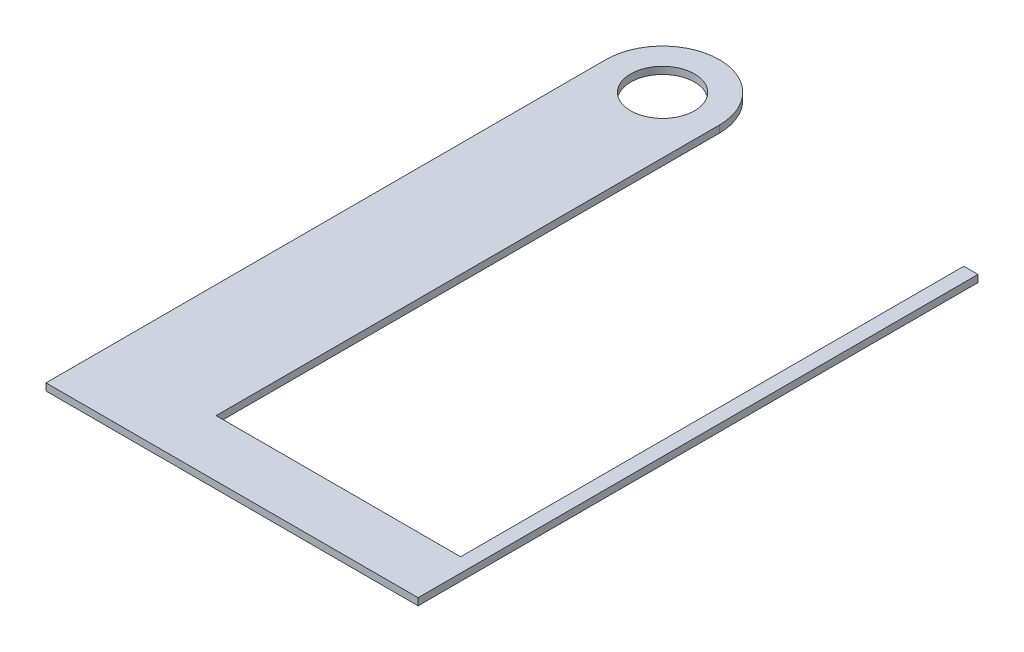
SolidWorks part; units mm, degrees
ref_plane "Front" through (0, 0, 0) normal (0, 0, 1) x (1, 0, 0)
ref_plane "Top" through (0, 0, 0) normal (0, 1, 0) x (1, 0, 0)
ref_plane "Right" through (0, 0, 0) normal (1, 0, 0) x (0, 0, -1)
sketch "Sketch1" plane through (0, 0, 0) normal (0, 1, 0) x (1, 0, 0)
  line L0 (-25.4, 0) -> (-25.4, -250.825)
  line L1 (-25.4, -250.825) -> (141.2875, -250.825)
  line L2 (141.2875, -250.825) -> (141.2875, 0)
  line L3 (141.2875, 0) -> (134.9375, 0)
  line L4 (134.9375, 0) -> (134.9375, -225.425)
  line L5 (134.9375, -225.425) -> (25.4, -225.425)
  line L6 (25.4, -225.425) -> (25.4, 0)
  line L8 (33.3375, -225.425) -> (134.9375, -225.425) construction
  line L9 (33.3375, -225.425) -> (33.3375, 76.2) construction
  line L10 (33.3375, 76.2) -> (134.9375, 76.2) construction
  line L11 (134.9375, -225.425) -> (134.9375, 76.2) construction
  line L12 (33.3375, -225.425) -> (134.9375, 76.2) construction
  line L13 (33.3375, 76.2) -> (134.9375, -225.425) construction
  circle A0 centre (0, 0) radius 14.3129
  arc A1 (25.4, 0) -> (-25.4, 0) centre (0, 0) ccw
  circle A2 centre (0, 0) radius 38.1 construction
  point P5 (84.1375, -74.6125)
  point P17 (134.9375, -250.825)
  dimension "D1" = 25.4
  dimension "D2" = 28.6258
  dimension "D7" = 76.2
  dimension "D8" = 9.525
  dimension "D3" = 6.35
  dimension "D4" = 25.4
  dimension "D5" = 101.6
  dimension "D6" = 301.625
  dimension "D9" = 76.2
extrude "Boss-Extrude1" add sketch "Sketch1" along normal blind 3.175
